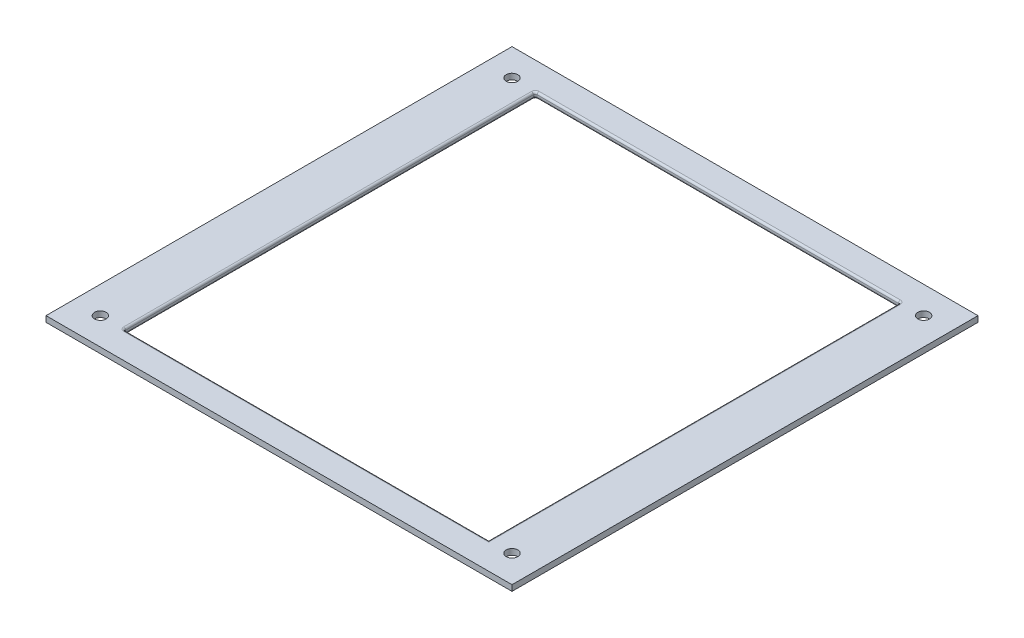
SolidWorks part; units mm, degrees
ref_plane "Front Plane" through (0, 0, 0) normal (0, 0, 1) x (1, 0, 0)
ref_plane "Top Plane" through (0, 0, 0) normal (0, 1, 0) x (1, 0, 0)
ref_plane "Right Plane" through (0, 0, 0) normal (1, 0, 0) x (0, 0, -1)
sketch "Sketch1" plane through (0, 0, 0) normal (0, 1, 0) x (1, 0, 0)
  line L1 (-60, -60) -> (60, -60)
  line L2 (-60, -60) -> (-60, 60)
  line L3 (-60, 60) -> (60, 60)
  line L4 (60, -60) -> (60, 60)
  line L5 (-60, -60) -> (60, 60) construction
  line L6 (-60, 60) -> (60, -60) construction
  point P0 (0, 0)
extrude "Boss-Extrude1" add sketch "Sketch1" along normal blind 1.5
sketch "Sketch2" plane through (0, 0, 0) normal (0, 1, 0) x (1, 0, 0)
  line L0 (-25, 0) -> (-25, 56.4247) construction
  line L1 (25, 0) -> (25, 58.8481) construction
  line L2 (0, 0) -> (0, 57.0064) construction
  line L3 (-20, 0) -> (-20, 37.3668) construction
  line L4 (20, 0) -> (20, 22.4016) construction
  line L5 (0, 0) -> (62.369, 0) construction
  line L6 (-22.5, 0) -> (-22.5, 36.1696) construction
  line L7 (22.5, 0) -> (22.5, 30.9816) construction
  dimension "D1" = 25
  dimension "D2" = 25
  dimension "D3" = 5
  dimension "D4" = 5
  dimension "D5" = 2.5
  dimension "D6" = 2.5
ref_point "Point1"
ref_point "Point2"
sketch "Sketch4" plane through (0, 0, 0) normal (0, 1, 0) x (1, 0, 0)
  circle A0 centre (-22.5, 0) radius 2.5
  circle A1 centre (22.5, 0) radius 2.5
extrude "Cut-Extrude2" cut sketch "Sketch4" along normal up to surface (1.5 mm away) up to face at (0, 1.5, 0)
sketch "Sketch5" plane through (0, 0, 0) normal (0, 1, 0) x (1, 0, 0)
  line L0 (-53, 0) -> (-53, 74.8856) construction
  line L1 (-55.2997, 53) -> (111.0551, 53) construction
  line L2 (53, 55.042) -> (53, 97.6787) construction
  line L3 (-55.2997, -53) -> (133.2261, -53) construction
  line L4 (-60, 60) -> (-60, -60) construction
  line L5 (60, -60) -> (60, 60) construction
  line L6 (-60, -60) -> (60, -60) construction
  line L7 (60, 60) -> (-60, 60) construction
  dimension "D1" = 7
  dimension "D2" = 7
  dimension "D3" = 7
  dimension "D4" = 7
ref_point "Point3"
ref_point "Point4"
ref_point "Point5"
ref_point "Point6"
sketch "Sketch7" plane through (0, 0, 0) normal (0, 1, 0) x (1, 0, 0)
  line L0 (-53, -200000) -> (-53, 200074.8856) construction
  line L1 (-200055.2997, -53) -> (200133.2261, -53) construction
  line L2 (53, -199944.958) -> (53, 200097.6787) construction
  circle A0 centre (-53, 53) radius 1.5
  circle A1 centre (53, 53) radius 1.5
  circle A2 centre (-53, -53) radius 1.5
  circle A3 centre (53, -53) radius 1.5
extrude "Cut-Extrude3" cut sketch "Sketch7" along normal up to surface (1.5 mm away) up to face at (-22.5, 1.5, -2.5)
sketch "Sketch8" plane through (0, 0, 0) normal (0, 1, 0) x (1, 0, 0)
  line L0 (-200055.2997, 53) -> (200111.0551, 53) construction
  line L1 (-47, 53) -> (47, 53)
  line L2 (-47, 53) -> (-47, -53)
  line L3 (-47, -53) -> (47, -53)
  line L4 (47, 53) -> (47, -53)
  line L5 (-200055.2997, -53) -> (200133.2261, -53) construction
  line L6 (-60, 60) -> (-60, -60) construction
  line L8 (60, -60) -> (60, 60) construction
  dimension "D1" = 13
  dimension "D2" = 13
extrude "Cut-Extrude4" cut sketch "Sketch8" along normal up to surface (1.5 mm away) up to face at (53, 1.5, -54.5)
fillet "Fillet1" radius 0.5 11 edges at (0, 1.5, 53) (0, 0, 53) (47, 1.5, 0) (47, 0, 0) (-47, 1.5, 0) (-47, 0, 0) (0, 1.5, -53) (0, 0, -53) (-47, 0.75, 53) (47, 0.75, -53) (-47, 0.75, -53)
